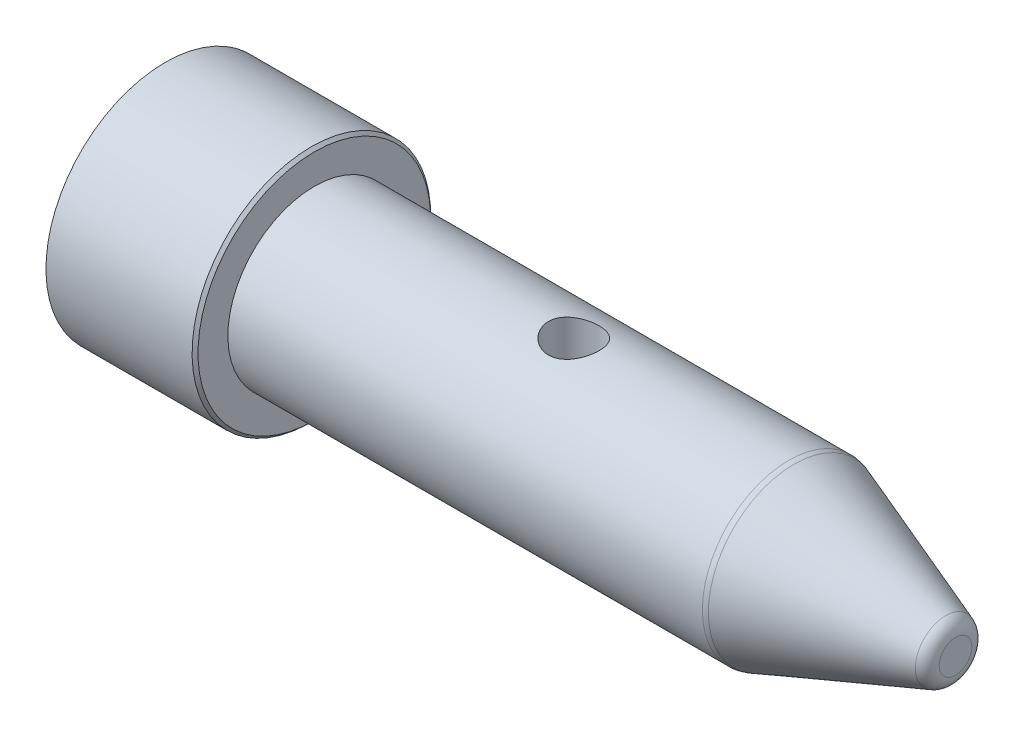
SolidWorks part; units mm, degrees
material "Group 2"
ref_plane "Front Plane" through (0, 0, 0) normal (0, 0, 1) x (1, 0, 0)
ref_plane "Top Plane" through (0, 0, 0) normal (0, 1, 0) x (1, 0, 0)
ref_plane "Right Plane" through (0, 0, 0) normal (1, 0, 0) x (0, 0, -1)
sketch "Skizze1" plane through (0, 0, 0) normal (0, 0, 1) x (1, 0, 0)
  line L0 (0, 40) -> (50, 40)
  line L1 (50, 40) -> (50, 29)
  line L2 (50, 29) -> (210, 29)
  line L3 (210, 29) -> (265, 8.9816)
  line L4 (265, 8.9816) -> (265, 0)
  line L5 (265, 0) -> (0, 0) construction
  line L6 (0, 10) -> (0, 40)
  line L7 (265, 0) -> (0, 0)
  line L8 (0, 10) -> (-3, 10)
  line L9 (-3, 10) -> (-3, 0)
  line L10 (-3, 0) -> (0, 0)
  point P2 (25, 40)
  dimension "D1" = 80
  dimension "D2" = 50
  dimension "D3" = 58
  dimension "D4" = 160
  dimension "D5" = 20
  dimension "D6" = 55
  dimension "D7" = 10
  dimension "D8" = 3
revolve "Rotation1" add sketch "Skizze1" angle 360 about L5
chamfer "Fase1" distance 1 angle 45 1 edges at (50, 40, 0)
fillet "Verrundung1" radius 5 2 edges at (265, 8.9816, 0) (210, 29, 0)
sketch "Skizze2" plane through (0, 0, 0) normal (0, 1, 0) x (1, 0, 0)
  circle A0 centre (137, 0) radius 8.5
  dimension "D1" = 17
  dimension "D2" = 137
extrude "Schnitt-Linear austragen1" cut sketch "Skizze2" against normal mid plane 110 contours A0
